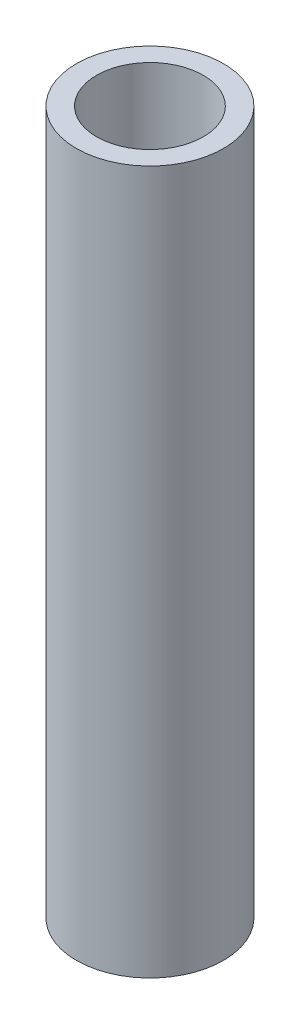
SolidWorks part; units mm, degrees
material "PVC Rigid"
ref_plane "Front" through (0, 0, 0) normal (0, 0, 1) x (1, 0, 0)
ref_plane "Top" through (0, 0, 0) normal (0, 1, 0) x (1, 0, 0)
ref_plane "Right" through (0, 0, 0) normal (1, 0, 0) x (0, 0, -1)
sketch "Sketch1" plane through (0, 0, 0) normal (0, 1, 0) x (1, 0, 0)
  circle A0 centre (0, 0) radius 10.615
  circle A1 centre (0, 0) radius 7.7
  dimension "D1" = 21.23
  dimension "D2" = 15.4
extrude "Boss-Extrude1" add sketch "Sketch1" along normal blind 101.5
sketch "Sketch2" plane through (0, 0, 0) normal (0, 1, 0) x (1, 0, 0)
  circle A0 centre (0, 0) radius 7.7
  circle A1 centre (0, 0) radius 3
  dimension "D1" = 15.4
  dimension "D2" = 6
extrude "Boss-Extrude2" add sketch "Sketch2" along normal blind 12.91 contours A0 A1
